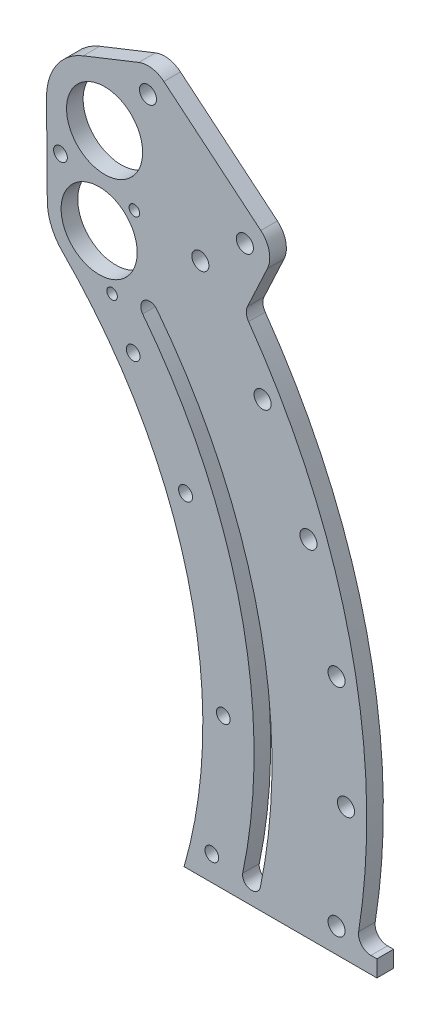
SolidWorks part; units mm, degrees
material "6061-T6 (SS)"
ref_plane "Front Plane" through (0, 0, 0) normal (0, 0, 1) x (1, 0, 0)
ref_plane "Top Plane" through (0, 0, 0) normal (0, 1, 0) x (1, 0, 0)
ref_plane "Right Plane" through (0, 0, 0) normal (1, 0, 0) x (0, 0, -1)
sketch "Sketch1" plane through (0, 0, 0) normal (0, 0, 1) x (1, 0, 0)
  line L0 (0, 0) -> (177.8, 0) construction
  line L1 (177.8, 0) -> (183.3563, 0) construction
  line L2 (0, 0) -> (191.1772, 6.6761) construction
  line L3 (0, 0) -> (182.7798, 182.7798) construction
  line L4 (184.7031, 10.1184) -> (184.959, 2.7905) construction
  line L5 (184.959, 2.7905) -> (191.4331, -0.6518) construction
  line L6 (191.4331, -0.6518) -> (197.6513, 3.2337) construction
  line L7 (197.6513, 3.2337) -> (197.3954, 10.5616) construction
  line L8 (197.3954, 10.5616) -> (190.9213, 14.0039) construction
  line L9 (190.9213, 14.0039) -> (184.7031, 10.1184) construction
  line L10 (156.6987, 109.7216) -> (0, 0) construction
  line L11 (0, 0) -> (176.7324, 73.2049) construction
  line L12 (183.3563, 0) -> (183.3563, -50.8) construction
  line L13 (176.1785, -50.8) -> (183.3563, -50.8) construction
  line L14 (0, 0) -> (186.7878, -41.275) construction
  line L15 (0, 0) -> (203.2, 0) construction
  line L16 (203.2, 0) -> (209.55, 0) construction
  line L17 (209.55, 0) -> (228.6, 0) construction
  line L18 (228.6, 0) -> (238.125, 0) construction
  line L19 (0, 0) -> (238.125, 0) construction
  line L20 (0, 0) -> (234.5073, 41.35) construction
  line L21 (176.1785, -50.8) -> (240.7615, -50.8)
  line L22 (0, 0) -> (238.125, 0) construction
  line L23 (0, 0) -> (234.5073, -41.35) construction
  line L24 (129.6524, 129.6524) -> (173.9925, 173.9925)
  line L25 (165.5338, 128.4903) -> (160.5177, 124.5966) construction
  line L26 (198.8628, -41.7593) -> (205.1195, -42.8625) construction
  arc A0 (183.3563, 0) -> (129.6524, 129.6524) centre (0, 0) ccw
  arc A1 (184.9438, 0) -> (130.775, 130.775) centre (0, 0) ccw construction
  circle A3 centre (191.1772, 6.6761) radius 6.35 construction
  circle A4 centre (191.1772, 6.6761) radius 2.6289
  circle A5 centre (156.6987, 109.7216) radius 2.6289
  circle A6 centre (176.7324, 73.2049) radius 2.667
  arc A7 (183.3563, 0) -> (176.1785, -50.8) centre (0, 0) cw
  circle A8 centre (186.7878, -41.275) radius 2.6289
  arc A9 (203.2, 0) -> (143.6841, 143.6841) centre (0, 0) ccw construction
  arc A10 (209.55, 0) -> (148.1742, 148.1742) centre (0, 0) ccw construction
  arc A11 (228.6, 0) -> (161.6446, 161.6446) centre (0, 0) ccw construction
  arc A12 (238.125, 0) -> (168.3798, 168.3798) centre (0, 0) ccw construction
  circle A13 centre (238.125, 0) radius 3.2639
  circle A14 centre (234.5073, 41.35) radius 3.2639
  circle A15 centre (223.7643, 81.4435) radius 3.2639
  circle A16 centre (206.2223, 119.0625) radius 3.2639
  circle A17 centre (182.4143, 153.0638) radius 3.2639
  arc A18 (240.7615, -50.8) -> (173.9925, 173.9925) centre (0, 0) ccw
  circle A19 centre (234.5073, -41.35) radius 3.2639
  arc A20 (209.55, 0) -> (165.5338, 128.4903) centre (0, 0) ccw construction
  arc A21 (160.5177, 124.5966) -> (203.2, 0) centre (0, 0) cw construction
  arc A22 (209.55, 0) -> (205.1195, -42.8625) centre (0, 0) cw construction
  arc A23 (203.2, 0) -> (198.8628, -41.7593) centre (0, 0) cw construction
  arc A24 (165.5338, 128.4903) -> (160.5177, 124.5966) centre (163.0257, 126.5435) ccw construction
  arc A25 (205.1195, -42.8625) -> (198.8628, -41.7593) centre (201.9911, -42.3109) cw construction
  arc A26 (202.946, 0) -> (198.6134, -41.711) centre (0, 0) cw
  arc A27 (205.3689, -42.9106) -> (198.6134, -41.711) centre (201.9911, -42.3109) cw
  arc A28 (209.804, 0) -> (205.3689, -42.9106) centre (0, 0) cw
  arc A29 (209.804, 0) -> (165.7345, 128.646) centre (0, 0) ccw
  arc A30 (165.7345, 128.646) -> (160.317, 124.4409) centre (163.0257, 126.5435) ccw
  arc A31 (160.317, 124.4409) -> (202.946, 0) centre (0, 0) cw
  point P9 (151.4971, 106.0794)
  point P20 (170.8657, 70.7749)
  point P27 (179.0372, -39.5623)
  dimension "D3" = 1.5875
  dimension "D4" = 12.7
  dimension "D6" = 5.2578
  dimension "D8" = 5.2578
  dimension "D12" = 5.334
  dimension "D14" = 50.8
  dimension "D15" = 5.2578
  dimension "D19" = 6.35
  dimension "D20" = 19.05
  dimension "D22" = 6.5278
  dimension "D26" = 7.9375
  dimension "D30" = 25.4
  dimension "D31" = 7.9375
  dimension "D33" = 183.3562
  dimension "D1" = 177.8
  dimension "D2" = 5.5562
  dimension "D5" = 2
  dimension "D7" = 45
  dimension "D9" = 6.35
  dimension "D10" = 10
  dimension "D11" = 22.5
  dimension "D13" = 6.35
  dimension "D16" = 9.525
  dimension "D17" = 7.9375
  dimension "D18" = 203.2
  dimension "D21" = 9.525
  dimension "D24" = 10
  dimension "D25" = 238.125
  dimension "D28" = 10
  dimension "D29" = 238.125
  dimension "D32" = 0.254
  dimension "D23" = 5
  dimension "D27" = 2
extrude "Boss-Extrude1" add sketch "Sketch1" along normal blind 6.35 contours L21 A18 L24 A0 A7 A19 A4 A5 A6 A8 A13 A14 A15 A16 A17 A22 A25 A23 A21 A24 A20
sketch "Sketch2" plane through (0, 0, 6.35) normal (0, 0, 1) x (1, 0, 0)
  line L0 (0, 0) -> (125.7236, 125.7236) construction
  line L1 (0, 0) -> (183.3562, 0) construction
  line L2 (125.7236, 125.7236) -> (143.6841, 143.6841) construction
  line L3 (129.6524, 129.6524) -> (173.9925, 173.9925) construction
  line L4 (143.6841, 143.6841) -> (145.7609, 177.9111) construction
  line L6 (0, 0) -> (145.7609, 177.9111) construction
  arc A0 (176.1785, -50.8) -> (129.6524, 129.6524) centre (0, 0) ccw construction
  circle A1 centre (143.6841, 143.6841) radius 14.5542
  circle A2 centre (143.6841, 143.6841) radius 25.4 construction
  circle A3 centre (143.6841, 143.6841) radius 11.43 construction
  circle A4 centre (143.6841, 143.6841) radius 19.05 construction
  circle A5 centre (145.7609, 177.9111) radius 22.86 construction
  circle A6 centre (145.7609, 177.9111) radius 14.5542
  dimension "D4" = 29.1084
  dimension "D5" = 50.8
  dimension "D6" = 22.86
  dimension "D7" = 38.1
  dimension "D8" = 45.72
  dimension "D9" = 229.997
  dimension "D10" = 29.1084
  dimension "D1" = 177.8
  dimension "D2" = 45
  dimension "D3" = 25.4
  dimension "D11" = 34.29
sketch "Sketch3" plane through (0, 0, 6.35) normal (0, 0, 1) x (1, 0, 0)
  line L0 (129.6524, 129.6524) -> (173.9925, 173.9925) construction
  line L1 (129.6524, 129.6524) -> (161.6446, 161.6446)
  line L4 (123.8411, 143.5075) -> (123.5368, 177.7134)
  line L5 (161.6446, 161.6446) -> (173.9925, 173.9925)
  line L6 (0, 0) -> (199.4397, 167.3498) construction
  line L7 (0, 0) -> (183.3562, 0) construction
  line L9 (208.0723, 163.3243) -> (199.2435, 144.391)
  line L10 (145.7609, 177.9111) -> (162.3612, 198.173) construction
  line L11 (0, 0) -> (145.7609, 177.9111) construction
  line L12 (137.5541, 198.5654) -> (158.844, 207.0248)
  line L13 (168.4502, 205.4976) -> (205.5286, 174.6744)
  line L14 (143.6841, 143.6841) -> (145.7609, 177.9111) construction
  line L15 (144.7225, 160.7976) -> (128.8766, 161.7591) construction
  arc A1 (129.6524, 129.6524) -> (123.8411, 143.5075) centre (143.6841, 143.6841) cw
  arc A2 (137.5541, 198.5654) -> (123.5368, 177.7134) centre (145.7609, 177.9111) ccw
  circle A3 centre (145.7609, 177.9111) radius 14.5542
  circle A4 centre (199.4397, 167.3498) radius 3.2639
  arc A5 (208.0723, 163.3243) -> (205.5286, 174.6744) centre (199.4397, 167.3498) ccw
  arc A7 (173.9925, 173.9925) -> (199.2435, 144.391) centre (0, 0) cw
  arc A8 (240.7615, -50.8) -> (173.9925, 173.9925) centre (0, 0) ccw construction
  circle A9 centre (162.3612, 198.173) radius 9.525 construction
  circle A10 centre (145.7609, 177.9111) radius 16.1417 construction
  circle A11 centre (162.3612, 198.173) radius 3.2639
  arc A12 (158.844, 207.0248) -> (168.4502, 205.4976) centre (162.3612, 198.173) cw
  circle A13 centre (128.8766, 161.7591) radius 2.6289
  circle A14 centre (128.8766, 161.7591) radius 3.9687 construction
  point P39 (148.964, 177.5652)
  point P40 (0, 0)
  point P41 (0, 0)
  point P42 (0, 0)
  dimension "D1" = 25.4
  dimension "D2" = 29.1084
  dimension "D3" = 22.225
  dimension "D5" = 260.35
  dimension "D6" = 6.5278
  dimension "D7" = 9.525
  dimension "D8" = 25
  dimension "D9" = 19.05
  dimension "D10" = 1.5875
  dimension "D11" = 6.5278
  dimension "D12" = 9.525
  dimension "D14" = 5.2578
  dimension "D15" = 7.9375
  dimension "D4" = 40
  dimension "D13" = 26.1937
  dimension "D16" = 15.875
extrude "Boss-Extrude2" add sketch "Sketch3" against normal blind 6.35
sketch "Sketch4" plane through (0, 0, 6.35) normal (0, 0, 1) x (1, 0, 0)
  line L0 (143.6841, 143.6841) -> (157.1545, 157.1545) construction
  line L1 (125.7236, 125.7236) -> (143.6841, 143.6841) construction
  line L2 (143.6841, 143.6841) -> (148.6146, 125.2832) construction
  circle A0 centre (143.6841, 143.6841) radius 14.5542
  circle A1 centre (157.1545, 157.1545) radius 2.0193
  circle A2 centre (148.6146, 125.2832) radius 2.0193
  dimension "D1" = 29.1084
  dimension "D2" = 4.0386
  dimension "D4" = 4.0386
  dimension "D3" = 19.05
  dimension "D5" = 19.05
  dimension "D6" = 60
extrude "Cut-Extrude1" cut sketch "Sketch4" against normal through all
sketch "Sketch5" plane through (0, 0, 6.35) normal (0, 0, 1) x (1, 0, 0)
  line L0 (240.7615, -50.8) -> (249.9519, -50.8)
  line L1 (249.9519, -50.8) -> (249.9519, -44.45)
  line L2 (249.9519, -44.45) -> (242.0144, -44.45)
  arc A0 (240.7615, -50.8) -> (199.2435, 144.391) centre (0, 0) ccw construction
  arc A1 (242.9628, -38.9339) -> (199.2435, 144.391) centre (0, 0) ccw construction
  arc A2 (242.0144, -44.45) -> (242.9628, -38.9339) centre (0, 0) ccw construction
  arc A3 (240.7615, -50.8) -> (242.0144, -44.45) centre (0, 0) ccw
  dimension "D2" = 6.35
  dimension "D3" = 7.9375
extrude "Boss-Extrude3" add sketch "Sketch5" against normal blind 6.35
fillet "Fillet1" radius 4.7625 1 edges at (242.0144, -44.45, 3.175)
fillet "Fillet2" radius 4.7625 1 edges at (199.2435, 144.391, 3.175)
